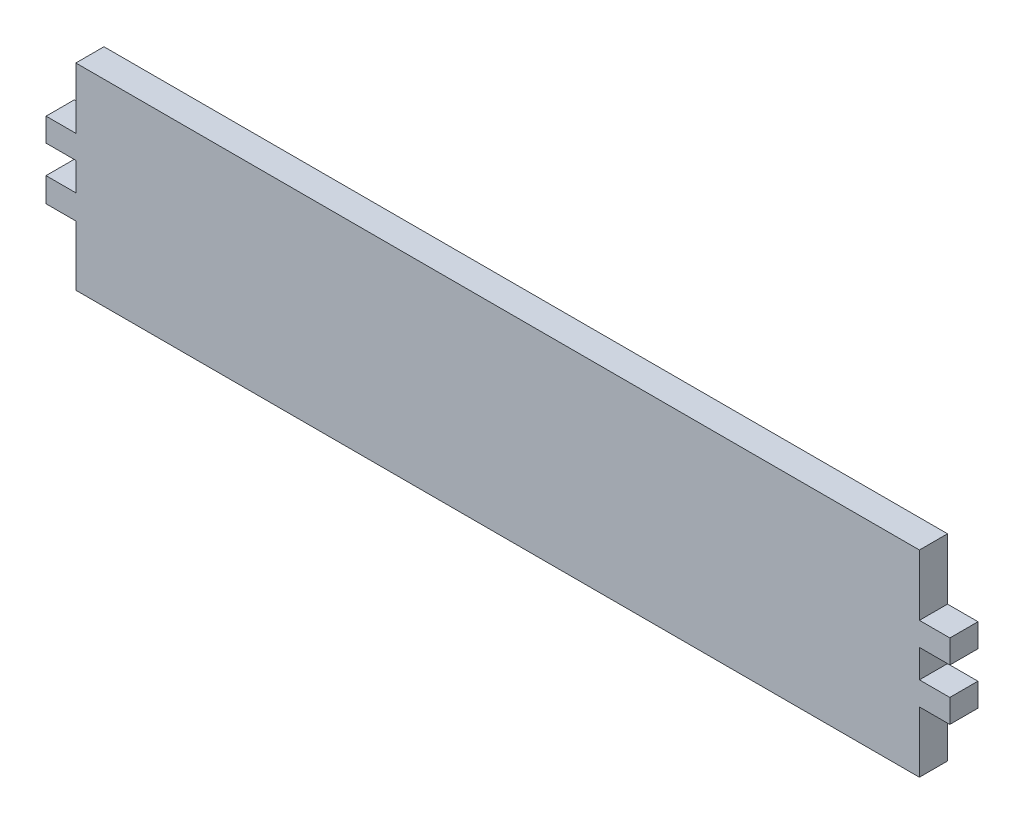
SolidWorks part; units mm, degrees
ref_plane "Front Plane" through (0, 0, 0) normal (0, 0, 1) x (1, 0, 0)
ref_plane "Top Plane" through (0, 0, 0) normal (0, 1, 0) x (1, 0, 0)
ref_plane "Right Plane" through (0, 0, 0) normal (1, 0, 0) x (0, 0, -1)
sketch "Sketch3" plane through (0, 0, 0) normal (0, 0, 1) x (1, 0, 0)
  line L0 (-59.9171, 29.2045) -> (120.0829, 29.2045)
  line L1 (120.0829, 29.2045) -> (120.0829, 16.2045)
  line L2 (120.0829, 16.2045) -> (126.5849, 16.2045)
  line L3 (126.5849, 16.2045) -> (126.5849, 11.2045)
  line L4 (126.5849, 11.2045) -> (120.0829, 11.2045)
  line L6 (120.0829, -12.7955) -> (120.0829, 0.2045)
  line L7 (120.0829, 0.2045) -> (126.5666, 0.2045)
  line L8 (126.5666, 0.2045) -> (126.5666, 5.2045)
  line L9 (126.5666, 5.2045) -> (120.0829, 5.2045)
  line L10 (120.0829, 5.2045) -> (120.0829, 11.2045)
  line L11 (120.0829, -12.7955) -> (-59.9171, -12.7955)
  line L12 (-59.9171, -12.7955) -> (-59.9171, 0)
  line L13 (-59.9171, 0) -> (-66.2861, 0)
  line L14 (-66.2861, 0) -> (-66.2861, 5.2045)
  line L15 (-66.2861, 5.2045) -> (-59.9171, 5.2045)
  line L16 (-59.9171, 5.2045) -> (-59.9171, 11.2045)
  line L17 (-59.9171, 11.2045) -> (-66.2684, 11.2045)
  line L18 (-66.2684, 11.2045) -> (-66.2684, 16.2045)
  line L19 (-66.2684, 16.2045) -> (-59.9171, 16.2045)
  line L20 (-59.9171, 16.2045) -> (-59.9171, 29.2045)
extrude "Boss-Extrude1" add sketch "Sketch3" along normal blind 6
